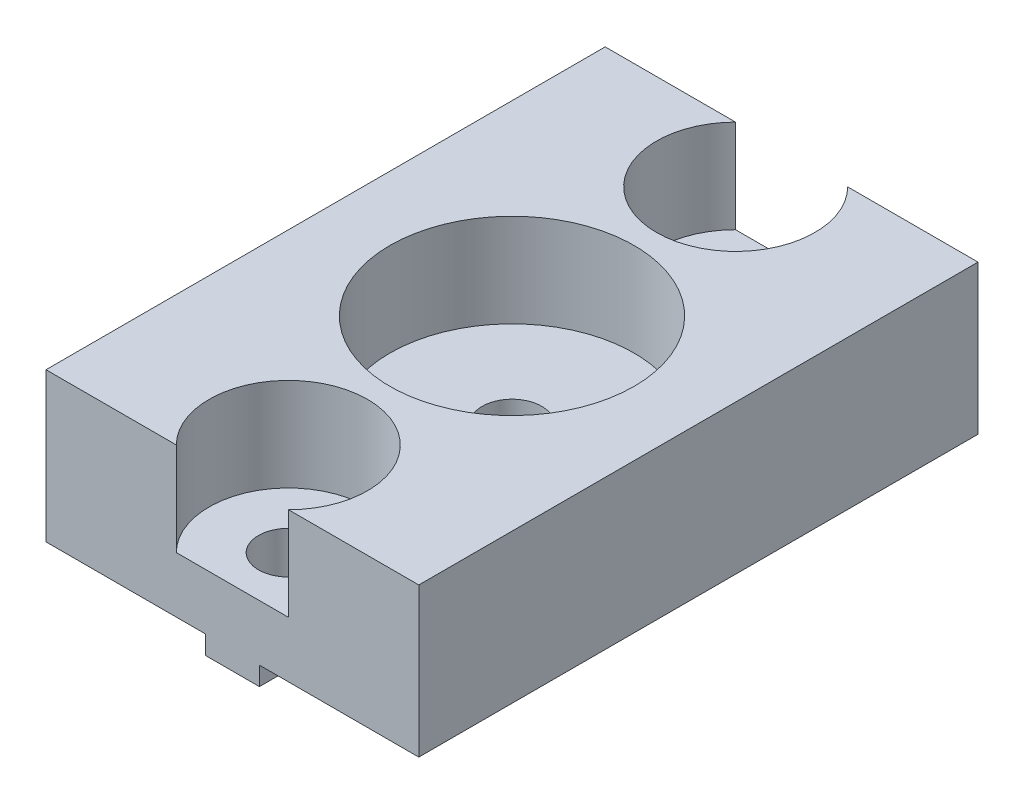
SolidWorks part; units mm, degrees
ref_plane "Front Plane" through (0, 0, 0) normal (0, 0, 1) x (1, 0, 0)
ref_plane "Top Plane" through (0, 0, 0) normal (0, 1, 0) x (1, 0, 0)
ref_plane "Right Plane" through (0, 0, 0) normal (1, 0, 0) x (0, 0, -1)
sketch "Sketch1" plane through (0, 0, 0) normal (0, 0, 1) x (1, 0, 0)
  line L0 (-10, 9) -> (10, 9)
  line L1 (10, 9) -> (10, 1)
  line L2 (10, 1) -> (1.45, 1)
  line L3 (1.45, 1) -> (1.45, 0)
  line L4 (1.45, 0) -> (-1.45, 0)
  line L5 (-1.45, 0) -> (-1.45, 1)
  line L6 (-1.45, 1) -> (-10, 1)
  line L7 (-10, 1) -> (-10, 9)
  point P8 (0, 0)
  point P9 (0, 0)
  point P10 (-5, 2.1563)
  point P12 (5, 2.4431)
  dimension "D1" = 20
  dimension "D2" = 8
  dimension "D3" = 2.9
  dimension "D4" = 1
extrude "Main" add sketch "Sketch1" along normal mid plane 30
sketch "Sketch5" plane through (0, 0, 0) normal (0, -1, 0) x (-1, 0, 0)
  line L0 (1.45, -15) -> (-1.45, -15) construction
  line L1 (1.45, 15) -> (-1.45, 15) construction
  circle A0 centre (0, 12) radius 1.6
  circle A1 centre (0, -12) radius 1.6
  circle A2 centre (0, 0) radius 1.6
  point P10 (0, 15)
  dimension "D1" = 3.2
  dimension "D2" = 3
  dimension "D3" = 3
extrude "FixHole" cut sketch "Sketch5" against normal through all
sketch "Sketch3" plane through (0, 9, 0) normal (0, 1, 0) x (1, 0, 0)
  circle A0 centre (0, 0) radius 6.55
  circle A1 centre (0, 12) radius 4.25
  circle A2 centre (0, -12) radius 4.25
  circle A3 centre (0, 12) radius 1.6 construction
  dimension "D1" = 13.1
  dimension "D2" = 8.5
extrude "BearingHole" cut sketch "Sketch3" against normal blind 5
